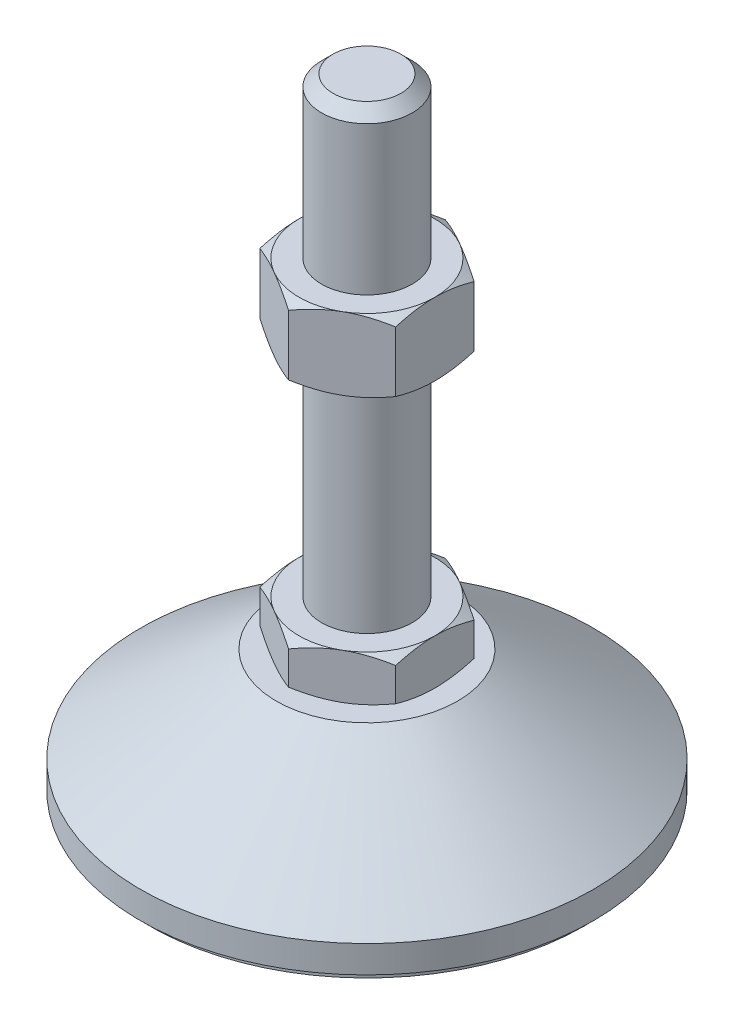
SolidWorks part; units mm, degrees
ref_plane "Спереди" through (0, 0, 0) normal (0, 0, 1) x (1, 0, 0)
ref_plane "Сверху" through (0, 0, 0) normal (0, 1, 0) x (1, 0, 0)
ref_plane "Справа" through (0, 0, 0) normal (1, 0, 0) x (0, 0, -1)
sketch "Эскиз1" plane through (0, 0, 0) normal (0, 0, 1) x (1, 0, 0)
  line L0 (0, 0) -> (-48, 0)
  line L1 (-48, 0) -> (-48, 2)
  line L2 (-48, 2) -> (-50, 2)
  line L3 (-50, 2) -> (-50, 8)
  line L4 (-50, 8) -> (-20, 29)
  line L5 (-20, 29) -> (-10, 29)
  line L12 (-10, 39) -> (-10, 136.5)
  line L13 (-10, 136.5) -> (-7.5, 139)
  line L14 (-7.5, 139) -> (0, 139)
  line L15 (0, 139) -> (0, 0) construction
  line L16 (-10, 29) -> (0, 29) construction
  line L17 (0, 0) -> (0, 139)
  line L18 (0, 0) -> (0, -7.9595) construction
  line L19 (-10, 39) -> (-10, 29)
  point P8 (-10, 87.75)
  point P23 (-15, 29)
  dimension "D1" = 20
  dimension "D2" = 29
  dimension "D3" = 10
  dimension "D4" = 100
  dimension "D5" = 10
  dimension "D6" = 2.5
  dimension "D7" = 45
  dimension "D8" = 40
  dimension "D9" = 2
  dimension "D10" = 100
  dimension "D11" = 6
revolve "Повернуть1" add sketch "Эскиз1" angle 360 about L17
sketch "Эскиз2" plane through (0, 29, 0) normal (0, 1, 0) x (1, 0, 0)
  line L1 (0, 17.3205) -> (-15, 8.6603)
  line L2 (-15, 8.6603) -> (-15, -8.6603)
  line L3 (-15, -8.6603) -> (0, -17.3205)
  line L4 (0, -17.3205) -> (15, -8.6603)
  line L5 (15, -8.6603) -> (15, 8.6603)
  line L6 (15, 8.6603) -> (0, 17.3205)
  circle A0 centre (0, 0) radius 15 construction
  dimension "D1" = 30
extrude "Бобышка-Вытянуть1" add sketch "Эскиз2" along normal up to vertex (10 mm away) up to point (-10, 39, 0)
ref_plane "Плоскость1" through (0, 87.75, 0) normal (0, 1, 0) x (1, 0, 0)
sketch "Эскиз3" plane through (0, 87.75, 0) normal (0, 1, 0) x (1, 0, 0)
  line L6 (15, 8.6603) -> (0, 17.3205)
  line L7 (0, 17.3205) -> (-15, 8.6603)
  line L8 (-15, 8.6603) -> (-15, -8.6603)
  line L9 (-15, -8.6603) -> (0, -17.3205)
  line L10 (0, -17.3205) -> (15, -8.6603)
  line L11 (15, -8.6603) -> (15, 8.6603)
  line L12 (15, 8.6603) -> (0, 17.3205)
  line L13 (0, 17.3205) -> (-15, 8.6603)
  line L14 (-15, 8.6603) -> (-15, -8.6603)
  line L15 (-15, -8.6603) -> (0, -17.3205)
  line L16 (0, -17.3205) -> (15, -8.6603)
  line L17 (15, -8.6603) -> (15, 8.6603)
  dimension "D1" = 0
extrude "Бобышка-Вытянуть2" add sketch "Эскиз3" along normal blind 16
sketch "Эскиз4" plane through (0, 0, 0) normal (0, 0, 1) x (1, 0, 0)
  line L0 (-15, 103.75) -> (-28.8564, 95.75)
  line L1 (-28.8564, 95.75) -> (-28.8564, 103.75)
  line L2 (-28.8564, 103.75) -> (-15, 103.75)
  line L3 (-28.8564, 95.75) -> (-15, 87.75)
  line L4 (50, 87.75) -> (-50, 87.75) construction
  line L5 (-15, 87.75) -> (-28.8564, 87.75)
  line L6 (-28.8564, 87.75) -> (-28.8564, 95.75)
  line L7 (-15, 103.75) -> (-15, 87.75) construction
  line L8 (-15, 39) -> (-23.6603, 39)
  line L9 (-23.6603, 39) -> (-23.6603, 34)
  line L10 (-23.6603, 34) -> (-15, 39)
  line L11 (-15, 29) -> (-23.6603, 34)
  line L12 (-23.6603, 34) -> (-23.6603, 29)
  line L13 (-23.6603, 29) -> (-15, 29)
  line L14 (0, 139) -> (0, 96.3793) construction
  dimension "D1" = 30
  dimension "D2" = 30
revolve "Вырез-Повернуть2" cut sketch "Эскиз4" angle 360 about L14
